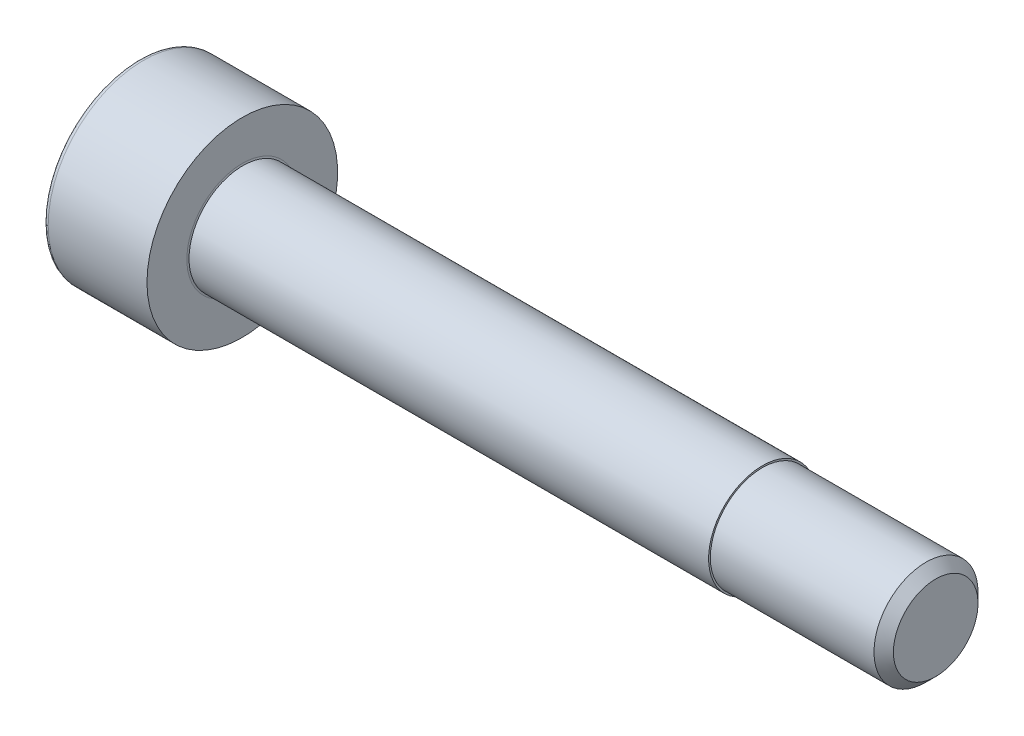
SolidWorks part; units mm, degrees
revolve "Base-Revolve" add sketch "BodySke"
sketch "BodySke" plane through (0, 0, 0) normal (0, 0, 1) x (1, 0, 0)
  line L0 (0, 0) -> (0, 2.75)
  line L1 (0, 2.75) -> (3, 2.75)
  line L2 (3, 2.75) -> (3, 1.5)
  line L3 (3, 1.5) -> (22.7195, 1.5)
  line L4 (23, 1.2195) -> (23, 0)
  line L5 (23, 0) -> (0, 0)
  line L6 (-31.75, 0) -> (127, 0) construction
  line L8 (23, 1.2195) -> (22.7195, 1.5)
  line L10 (23, -1.2195) -> (22.7195, -1.5) construction
  line L11 (3.5, 9.525) -> (3.5, 3.175) construction
  line L12 (3, 9.525) -> (3, 3.175) construction
  line L13 (-37, 9.525) -> (-37, 3.175) construction
  dimension "Head_ht" = 3
  dimension "Length" = 20
  dimension "Body_ch_ang" = 45
  dimension "Diameter" = 3
  dimension "Minor_dia" = 2.439
  dimension "Advance" = 0.5
  dimension "Thread_nom" = 20
  dimension "Thread_length" = 60
  dimension "Head_dia" = 5.5
cosmetic thread "ThreadCosmetic"
fillet "Fillet1" radius 0.1 1 edges at (3, 0, 1.5)
fillet "Fillet2" radius 0.15 1 edges at (0, 0, 2.75)
ref_plane "Plane1" through (0, 0, 0) normal (0, 0, 1) x (1, 0, 0)
ref_plane "Plane2" through (0, 0, 0) normal (0, 1, 0) x (1, 0, 0)
ref_plane "Plane3" through (0, 0, 0) normal (1, 0, 0) x (0, 0, -1)
sketch "Sketch2" plane through (0, 0, 0) normal (0, 0, 1) x (1, 0, 0)
  line L0 (0, 1.28) -> (1.3, 1.28)
  line L1 (1.3, 1.28) -> (2.039, 0)
  line L2 (-31.75, 0) -> (127, 0) construction
  line L3 (2.039, 0) -> (0, 0)
  line L4 (0, 0) -> (0, 1.28)
  line L6 (0, 0) -> (47.625, 0) construction
  dimension "D1" = 1.28
  dimension "D2" = 60
  dimension "Depth" = 1.3
revolve "Hex-PreBroach" cut sketch "Sketch2" angle 360 about L6
sketch "Sketch3" plane through (0, 0, 0) normal (-1, 0, 0) x (0, 0.5, 0.866)
  line L0 (0.739, 1.28) -> (-0.739, 1.28)
  line L1 (-0.739, 1.28) -> (-1.478, 0)
  line L2 (0.739, 1.28) -> (1.478, 0)
  line L3 (0.739, -1.28) -> (1.478, 0)
  line L4 (0.739, -1.28) -> (-0.739, -1.28)
  line L5 (-0.739, -1.28) -> (-1.478, 0)
  dimension "D1" = 1.28
  dimension "D2" = 1.28
  dimension "Hex_size" = 2.56
extrude "Hex" cut sketch "Sketch3" against normal blind 1.3
sketch "ThdSchSke" plane through (0, 0, 0) normal (0, 0, 1) x (1, 0, 0)
  line L0 (4.5, -1.2195) -> (4.3036, -1.5)
  line L1 (4.5, -1.2195) -> (4.6964, -1.5)
  line L2 (4.6964, -1.5) -> (4.6964, -1.875)
  line L3 (-3.175, 0) -> (5.1513, 0) construction
  line L4 (0, 2.6) -> (0, -2.6) construction
  line L5 (4.6964, -1.875) -> (4.3036, -1.875)
  line L6 (4.3036, -1.875) -> (4.3036, -1.5)
  dimension "Thread_minor" = 2.439
  dimension "Diameter" = 3
  dimension "Start" = 4.5
revolve "ThreadSchematic" [suppressed] cut sketch "ThdSchSke" angle 360 about L3
pattern_linear "ThdSchPat" [suppressed]
sketch "Sketch4" plane through (3, 0, 0) normal (1, 0, 0) x (0, 0, -1)
  circle A0 centre (0, 0) radius 1.55
extrude "Boss-Extrude1" add sketch "Sketch4" along normal blind 15
equation "\"D2@Sketch3\" = \"Hex_size@Sketch3\" / 2"
equation "\"D1@Sketch3\" = \"Hex_size@Sketch3\" / 2"
equation "\"D1@Sketch2\" = \"Hex_size@Sketch3\" / 2"
equation "\"Thread_minor@ThreadCosmetic\"  =  \"Minor_dia@BodySke\""
equation "\"Depth@Sketch2\" =  \"Key_eng@Hex\""
equation "\"Thread_length@ThreadCosmetic\" = ((sgn( (\"Length@BodySke\" - \"Advance@BodySke\" * 3.0) - \"Thread_nom@BodySke\" )-1)*( (\"Length@BodySke\" - \"Advance@BodySke\" * 3.0) - \"Thread_nom@BodySke\" ))/-2+ \"Thread_nom@BodySke\""
equation "\"Thread_minor@ThdSchSke\" = \"Minor_dia@BodySke\""
equation "\"Diameter@ThdSchSke\" = \"Diameter@BodySke\""
equation "\"Overcut@ThdSchSke\" = \"Diameter@BodySke\" * 1.25"
equation "\"Start@ThdSchSke\" = \"Head_ht@BodySke\" + \"Length@BodySke\" - \"Thread_length@ThreadCosmetic\"  '---Non-countersunk---"
equation "\"Num_threads@ThdSchPat\" = int( \"Thread_length@ThreadCosmetic\" / \"Advance@BodySke\" + 0.999 )  + 1"
equation "\"Advance@ThdSchPat\" = \"Thread_length@ThreadCosmetic\" /  (\"Num_threads@ThdSchPat\" - 1) 'relax it"
equation "\"Num_threads@ThdSchPat\" = \"Num_threads@ThdSchPat\" - sgn( \"Num_threads@ThdSchPat\" - 1) '---chamfered tips only---"
